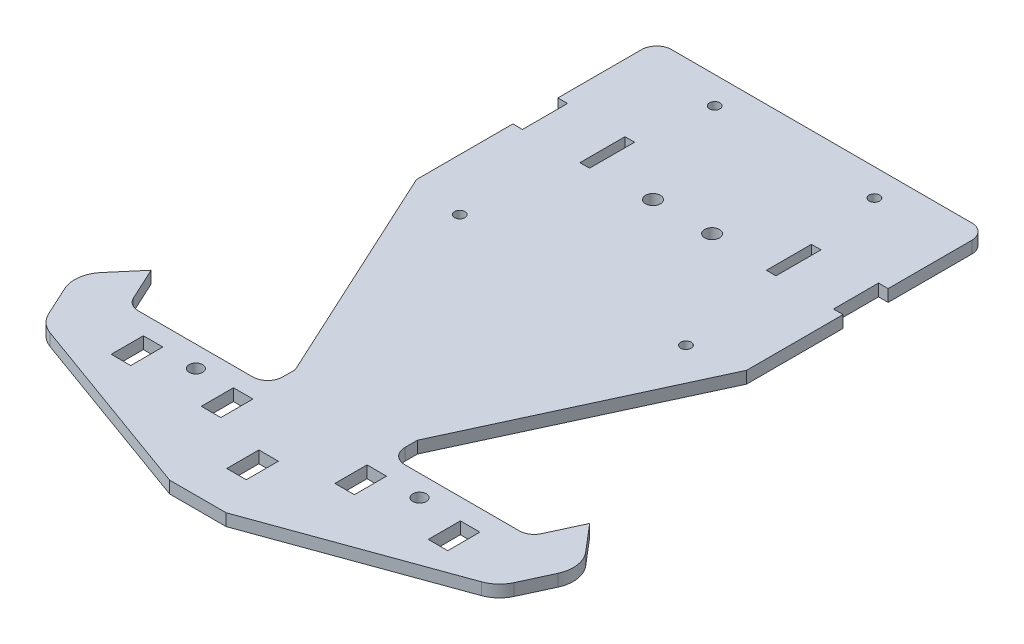
SolidWorks part; units mm, degrees
ref_plane "Front Plane" through (0, 0, 0) normal (0, 0, 1) x (1, 0, 0)
ref_plane "Top Plane" through (0, 0, 0) normal (0, 1, 0) x (1, 0, 0)
ref_plane "Right Plane" through (0, 0, 0) normal (1, 0, 0) x (0, 0, -1)
ref_plane "Plane1" through (0, -35, 0) normal (0, 1, 0) x (1, 0, 0)
sketch "Sketch1" plane through (0, -35, 0) normal (0, 1, 0) x (1, 0, 0)
  line L0 (0, 0) -> (0, 76.2257) construction
  line L1 (0, 0) -> (0, -148.2044) construction
  line L2 (-50, 76.2257) -> (50, 76.2257)
  line L4 (55, -3.7743) -> (20.3479, -78.7743)
  line L5 (20.3479, -78.7743) -> (20.3479, -82.9565)
  line L6 (67.9785, -85.0536) -> (73.0383, -74.1022)
  line L7 (25.3479, -87.9565) -> (63.4395, -87.9565)
  line L26 (-20.3479, -78.7743) -> (-20.3479, -82.9565)
  line L27 (-55, -3.7743) -> (-20.3479, -78.7743)
  line L28 (-55, 71.2257) -> (-55, -3.7743)
  line L29 (73.0383, -74.1022) -> (80.6854, -83.0863)
  line L30 (82.1483, -93.7622) -> (77.535, -103.7471)
  line L31 (71.8609, -108.9557) -> (9.4029, -131.5658)
  line L32 (-9.4029, -131.5658) -> (9.4029, -131.5658)
  line L33 (-71.8609, -108.9557) -> (-9.4029, -131.5658)
  line L34 (-82.1483, -93.7622) -> (-77.535, -103.7471)
  line L35 (-73.0383, -74.1022) -> (-80.6854, -83.0863)
  line L36 (-25.3479, -87.9565) -> (-63.4395, -87.9565)
  line L37 (-67.9785, -85.0536) -> (-73.0383, -74.1022)
  line L38 (55, 71.2257) -> (55, -3.7743)
  line L39 (-55.4335, -94.2938) -> (-55.4335, -104.9938)
  line L40 (-54.4335, -95.2938) -> (-49.9335, -95.2938) construction
  line L41 (-54.4335, -95.2938) -> (-54.4335, -103.9938) construction
  line L42 (-54.4335, -103.9938) -> (-49.9335, -103.9938) construction
  line L43 (-49.9335, -95.2938) -> (-49.9335, -103.9938) construction
  line L44 (-55.4335, -104.9938) -> (-48.9335, -104.9938)
  line L45 (-48.9335, -94.2938) -> (-48.9335, -104.9938)
  line L46 (-55.4335, -94.2938) -> (-48.9335, -94.2938)
  line L47 (24.5665, -95.7938) -> (24.5665, -103.9938) construction
  line L48 (-24.4335, -95.2938) -> (-19.9335, -95.2938) construction
  line L49 (-24.4335, -95.2938) -> (-24.4335, -103.9938) construction
  line L50 (-24.4335, -103.9938) -> (-19.9335, -103.9938) construction
  line L51 (-19.9335, -95.2938) -> (-19.9335, -103.9938) construction
  line L52 (20.0665, -95.2938) -> (24.5665, -95.2938) construction
  line L53 (20.0665, -95.2938) -> (20.0665, -103.9938) construction
  line L54 (20.0665, -103.9938) -> (24.5665, -103.9938) construction
  line L55 (24.5665, -95.2938) -> (24.5665, -103.9938) construction
  line L56 (-25.4335, -94.2938) -> (-18.9335, -94.2938)
  line L57 (51.7665, -95.8938) -> (56.2665, -95.8938) construction
  line L58 (51.7665, -95.8938) -> (51.7665, -104.5938) construction
  line L59 (51.7665, -104.5938) -> (56.2665, -104.5938) construction
  line L60 (56.2665, -95.8938) -> (56.2665, -104.5938) construction
  line L65 (-18.9335, -94.2938) -> (-18.9335, -104.9938)
  line L66 (-25.4335, -104.9938) -> (-18.9335, -104.9938)
  line L67 (-25.4335, -94.2938) -> (-25.4335, -104.9938)
  line L68 (19.0665, -94.2938) -> (25.5665, -94.2938)
  line L69 (25.5665, -94.2938) -> (25.5665, -104.9938)
  line L70 (19.0665, -104.9938) -> (25.5665, -104.9938)
  line L71 (19.0665, -94.2938) -> (19.0665, -104.9938)
  line L72 (50.7665, -94.8938) -> (57.2665, -94.8938)
  line L73 (57.2665, -94.8938) -> (57.2665, -105.5938)
  line L74 (50.7665, -105.5938) -> (57.2665, -105.5938)
  line L75 (50.7665, -94.8938) -> (50.7665, -105.5938)
  line L86 (-3.25, -107.9938) -> (3.25, -107.9938)
  line L87 (-3.25, -107.9938) -> (-3.25, -118.6938)
  line L88 (-3.25, -118.6938) -> (3.25, -118.6938)
  line L89 (3.25, -107.9938) -> (3.25, -118.6938)
  line L90 (-3.25, -107.9938) -> (3.25, -118.6938) construction
  line L91 (-3.25, -118.6938) -> (3.25, -107.9938) construction
  arc A4 (-71.8609, -108.9557) -> (-77.535, -103.7471) centre (-68.4571, -99.5529) cw
  arc A5 (77.535, -103.7471) -> (71.8609, -108.9557) centre (68.4571, -99.5529) cw
  arc A6 (80.6854, -83.0863) -> (82.1483, -93.7622) centre (73.0704, -89.568) cw
  arc A7 (-82.1483, -93.7622) -> (-80.6854, -83.0863) centre (-73.0704, -89.568) cw
  arc A8 (50, 76.2257) -> (55, 71.2257) centre (50, 71.2257) cw
  arc A9 (-55, 71.2257) -> (-50, 76.2257) centre (-50, 71.2257) cw
  arc A10 (63.4395, -87.9565) -> (67.9785, -85.0536) centre (63.4395, -82.9565) ccw
  arc A11 (-63.4395, -87.9565) -> (-67.9785, -85.0536) centre (-63.4395, -82.9565) cw
  arc A12 (20.3479, -82.9565) -> (25.3479, -87.9565) centre (25.3479, -82.9565) ccw
  arc A13 (-25.3479, -87.9565) -> (-20.3479, -82.9565) centre (-25.3479, -82.9565) ccw
  circle A14 centre (-37.2335, -94.9938) radius 2.25
  circle A15 centre (37.2665, -94.9938) radius 2.25
  point P15 (0, -113.3438)
  point P23 (-75.7847, -107.5353)
  point P26 (75.7847, -107.5353)
  point P30 (84.8307, -87.9565)
  point P33 (-84.8307, -87.9565)
  point P36 (55, 76.2257)
  point P39 (-55, 76.2257)
  point P41 (66.6373, -87.9565)
  point P47 (-66.6373, -87.9565)
  point P50 (20.3479, -87.9565)
  point P53 (-20.3479, -87.9565)
  dimension "D1" = 10
  dimension "D2" = 5
  dimension "D6" = 5
  dimension "D3" = 110
  dimension "D4" = 80
  dimension "D5" = 75
  dimension "D11" = 10.7
  dimension "D9" = 3
  dimension "D10" = 6.5
  dimension "D7" = 1
  dimension "D8" = 1
extrude "Boss-Extrude1" add sketch "Sketch1" along normal mid plane 4
sketch "Sketch3" plane through (0, -37, 0) normal (0, -1, 0) x (1, 0, 0)
  line L0 (0, -76.2257) -> (0, 160.862) construction
  line L1 (50, -76.2257) -> (-50, -76.2257) construction
  line L2 (63.4395, 87.9565) -> (25.3479, 87.9565) construction
  line L3 (-2, 87.9565) -> (-2, 72.9565)
  line L4 (2, 87.9565) -> (2, 72.9565)
  line L5 (-2, 87.9565) -> (2, 87.9565)
  line L6 (2, 72.9565) -> (-2, 72.9565)
  point P5 (0, 87.9565)
  dimension "D1" = 15
  dimension "D2" = 4
extrude "Boss-Extrude2" add sketch "Sketch3" along normal blind 16
fillet "Fillet1" radius 10 1 edges at (0, -53, 87.9565)
fillet "Fillet2" radius 4 1 edges at (0, -53, 72.9565)
chamfer "Chamfer1" distance 3 angle 60 4 edges at (0, -37, 87.9565) (2, -37, 80.4565) (0, -37, 72.9565) (-2, -37, 80.4565)
sketch "Sketch7" plane through (-2, 0, 0) normal (-1, 0, 0) x (0, 0, 1)
  line L4 (87.9565, -43) -> (87.9565, -42.1962)
  line L5 (87.9565, -42.1962) -> (72.9565, -42.1962)
  line L6 (72.9565, -42.1962) -> (72.9565, -49)
  line L7 (76.9565, -53) -> (77.9565, -53)
  line L8 (87.9565, -43) -> (87.9565, -42.1962)
  line L9 (87.9565, -42.1962) -> (72.9565, -42.1962)
  line L10 (72.9565, -42.1962) -> (72.9565, -49)
  line L11 (76.9565, -53) -> (77.9565, -53)
  arc A2 (72.9565, -49) -> (76.9565, -53) centre (76.9565, -49) ccw
  arc A3 (77.9565, -53) -> (87.9565, -43) centre (77.9565, -43) ccw
  arc A4 (72.9565, -49) -> (76.9565, -53) centre (76.9565, -49) ccw
  arc A5 (77.9565, -53) -> (87.9565, -43) centre (77.9565, -43) ccw
  spline S0 degree 2 poles (72.9565, -42.1962) (75.353, -47.9946) (72.9565, -49) knots 0 0 0 0.70445 0.70445 0.70445
  dimension "D1" = 0
extrude "Cut-Extrude2" cut sketch "Sketch7" against normal blind 16 contours L4 L7
sketch "Sketch10" plane through (0, -37, 0) normal (0, -1, 0) x (1, 0, 0)
  line L0 (-33.3236, -67.5888) -> (-51.1236, -67.5888) construction
  line L1 (-55, -28.3474) -> (-51.8, -28.3474)
  line L2 (-55, -28.3474) -> (-55, -43.3474)
  line L3 (-55, -43.3474) -> (-51.8, -43.3474)
  line L4 (-51.8, -28.3474) -> (-51.8, -43.3474)
  line L7 (-42.2236, -67.5888) -> (-42.2236, -32.1492) construction
  line L8 (-29.4471, -43.3474) -> (-32.6471, -43.3474)
  line L10 (-32.6471, -28.3474) -> (-32.6471, -43.3474)
  line L11 (-29.4471, -28.3474) -> (-32.6471, -28.3474)
  line L12 (-29.4471, -28.3474) -> (-29.4471, -43.3474)
  line L13 (0, -76.2257) -> (0, 66.3536) construction
  line L14 (50, -76.2257) -> (-50, -76.2257) construction
  line L15 (29.4471, -28.3474) -> (29.4471, -43.3474)
  line L16 (29.4471, -28.3474) -> (32.6471, -28.3474)
  line L17 (32.6471, -28.3474) -> (32.6471, -43.3474)
  line L18 (29.4471, -43.3474) -> (32.6471, -43.3474)
  line L19 (55, -43.3474) -> (51.8, -43.3474)
  line L20 (51.8, -28.3474) -> (51.8, -43.3474)
  line L21 (55, -28.3474) -> (51.8, -28.3474)
  line L22 (55, -28.3474) -> (55, -43.3474)
  circle A0 centre (-9.8389, -29.8685) radius 1.9684 construction
  circle A1 centre (-9.8389, -29.8685) radius 2.4684
  circle A2 centre (9.8389, -29.8685) radius 2.4684
  circle A3 centre (-37.674, 6.6651) radius 1.75
  circle A4 centre (-26.592, -67.1804) radius 1.75
  circle A5 centre (37.674, 6.6651) radius 1.75
  circle A6 centre (26.592, -67.1804) radius 1.75
  dimension "D4" = 3.5
  dimension "D5" = 3.5
  dimension "D1" = 3.2
  dimension "D2" = 15
  dimension "D3" = 0.5
extrude "Cut-Extrude3" cut sketch "Sketch10" against normal blind 4
ref_plane "Plane2" through (0, -37, 0) normal (0, -1, 0) x (-1, 0, 0)
sketch "Sketch12" plane through (0, -37, 0) normal (0, -1, 0) x (-1, 0, 0)
  line L1 (-25.9237, -45.2861) -> (27.354, -45.2861)
  line L2 (-25.9237, -45.2861) -> (-25.9237, -113.5817)
  line L3 (-25.9237, -113.5817) -> (27.354, -113.5817)
  line L4 (27.354, -45.2861) -> (27.354, -113.5817)
extrude "Cut-Extrude4" cut sketch "Sketch12" along normal blind 23
